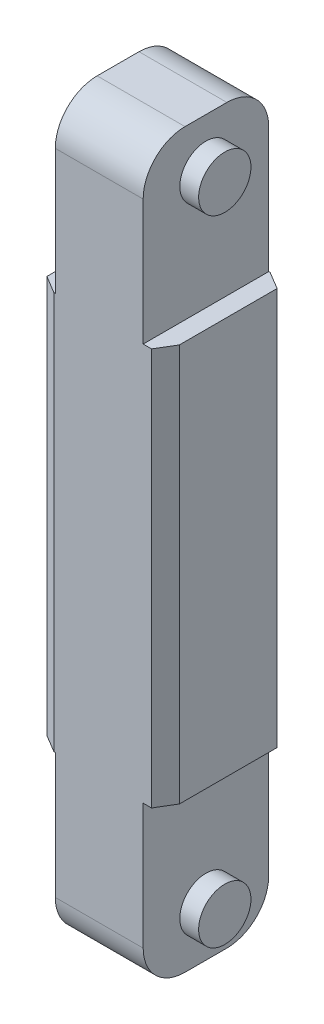
SolidWorks part; units mm, degrees
ref_plane "Front Plane" through (0, 0, 0) normal (0, 0, 1) x (1, 0, 0)
ref_plane "Top Plane" through (0, 0, 0) normal (0, 1, 0) x (1, 0, 0)
ref_plane "Right Plane" through (0, 0, 0) normal (1, 0, 0) x (0, 0, -1)
sketch "Sketch1" plane through (0, 0, 0) normal (0, 1, 0) x (1, 0, 0)
  line L1 (-60, 60) -> (60, 60)
  line L2 (-60, 60) -> (-60, -60)
  line L3 (-60, -60) -> (60, -60)
  line L4 (60, 60) -> (60, -60)
  line L5 (-60, 60) -> (60, -60) construction
  line L6 (-60, -60) -> (60, 60) construction
  point P0 (0, 0)
  dimension "D1" = 120
  dimension "D2" = 120
extrude "Boss-Extrude1" add sketch "Sketch1" along normal blind 700
sketch "Sketch2" plane through (0, 0, 0) normal (0, -1, 0) x (1, 0, 0)
  line L0 (0, -60) -> (0, 60) construction
  line L1 (60, -60) -> (-60, -60) construction
  line L2 (-60, 60) -> (60, 60) construction
  line L3 (-60, 60) -> (-42, 60)
  line L4 (60, -60) -> (42, -60)
  line L5 (60, -60) -> (60, 60)
  line L6 (60, 60) -> (42, 60)
  line L7 (42, -60) -> (42, 60)
  line L8 (-60, -60) -> (-42, -60)
  line L9 (-60, -60) -> (-60, 60)
  line L10 (-42, -60) -> (-42, 60)
  dimension "D1" = 18
extrude "Cut-Extrude1" cut sketch "Sketch2" against normal blind 160
sketch "Sketch3" plane through (-42, 0, 0) normal (-1, 0, 0) x (0, 0, 1)
  line L0 (-60, 0) -> (60, 0) construction
  circle A0 centre (0, 47.02) radius 26.2285
  dimension "D1" = 47.02
  dimension "D2" = 60
extrude "Boss-Extrude2" add sketch "Sketch3" along normal blind 18
sketch "Sketch4" plane through (42, 0, 0) normal (1, 0, 0) x (0, 0, -1)
  line L0 (-60, 0) -> (60, 0) construction
  line L1 (-60, 160) -> (-60, 0) construction
  circle A0 centre (0, 47.02) radius 25
  dimension "D1" = 50
  dimension "D2" = 47.02
  dimension "D3" = 60
extrude "Boss-Extrude3" add sketch "Sketch4" along normal blind 18
fillet "Fillet1" radius 40 2 edges at (0, 0, 60) (0, 0, -60)
sketch "Sketch5" plane through (0, 700, 0) normal (0, 1, 0) x (1, 0, 0)
  line L0 (-60, -60) -> (60, -60) construction
  line L1 (-60, 60) -> (-42, 60)
  line L2 (-60, 60) -> (-60, -60)
  line L3 (-60, -60) -> (-42, -60)
  line L4 (-42, 60) -> (-42, -60)
  line L5 (0, 60) -> (0, -60) construction
  line L6 (60, 60) -> (-60, 60) construction
  line L7 (60, -60) -> (42, -60)
  line L8 (42, 60) -> (42, -60)
  line L9 (60, 60) -> (42, 60)
  line L10 (60, 60) -> (60, -60)
  dimension "D1" = 18
extrude "Cut-Extrude2" cut sketch "Sketch5" against normal blind 160 contours L2 L1 L4 L3 | L7 L8 L9 L10
sketch "Sketch6" plane through (-42, 0, 0) normal (-1, 0, 0) x (0, 0, 1)
  line L0 (-60, 540) -> (-60, 700) construction
  line L1 (-60, 700) -> (60, 700) construction
  circle A0 centre (0, 652.98) radius 25
  dimension "D1" = 50
  dimension "D2" = 60
  dimension "D3" = 47.02
extrude "Boss-Extrude5" add sketch "Sketch6" along normal blind 18
sketch "Sketch7" plane through (42, 0, 0) normal (1, 0, 0) x (0, 0, -1)
  line L0 (60, 700) -> (-60, 700) construction
  line L1 (60, 540) -> (60, 700) construction
  circle A0 centre (0, 652.98) radius 25
  dimension "D1" = 50
  dimension "D2" = 47.02
  dimension "D3" = 60
extrude "Boss-Extrude6" add sketch "Sketch7" along normal blind 18
fillet "Fillet2" radius 40 2 edges at (0, 700, 60) (0, 700, -60)
chamfer "Chamfer1" distance 10 angle 59 4 edges at (60, 350, -60) (60, 350, 60) (-60, 350, -60) (-60, 350, 60)
